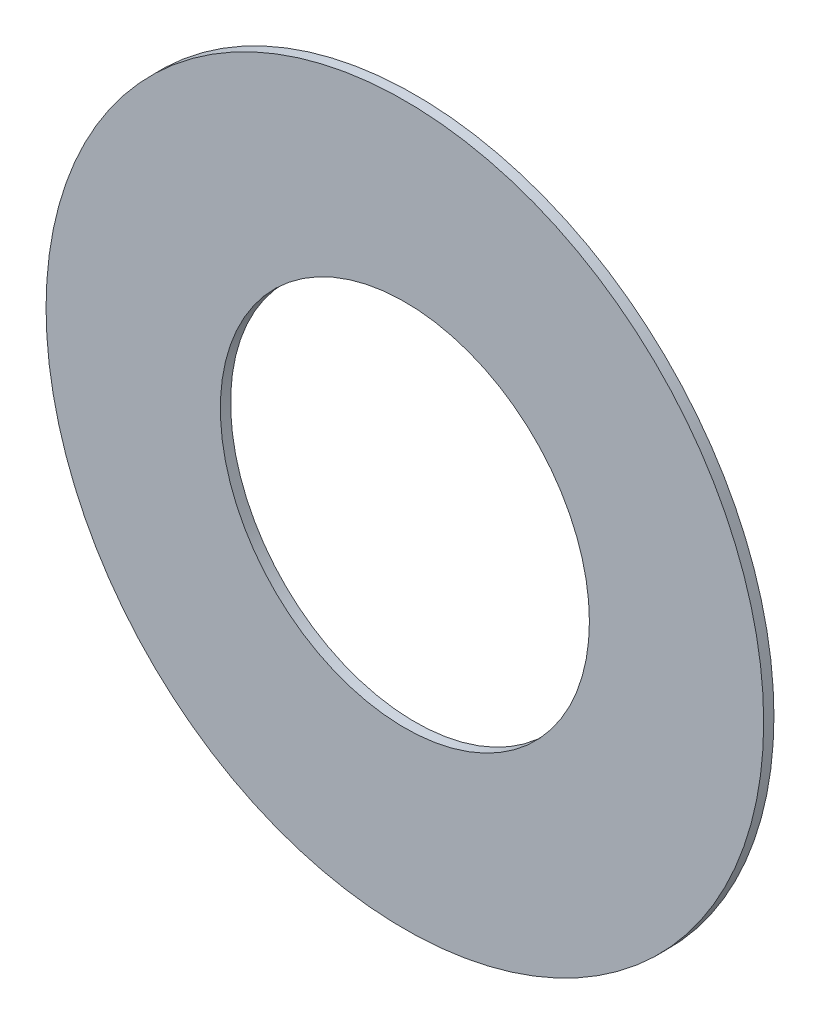
SolidWorks part; units mm, degrees
ref_plane "Front Plane" through (0, 0, 0) normal (0, 0, 1) x (1, 0, 0)
ref_plane "Top Plane" through (0, 0, 0) normal (0, 1, 0) x (1, 0, 0)
ref_plane "Right Plane" through (0, 0, 0) normal (1, 0, 0) x (0, 0, -1)
sketch "Sketch1" plane through (0, 0, 0) normal (0, 0, 1) x (1, 0, 0)
  circle A0 centre (0, 0) radius 36
  circle A1 centre (0, 0) radius 70
  dimension "D1" = 72
  dimension "D2" = 140
extrude "Boss-Extrude1" add sketch "Sketch1" along normal blind 2
sketch "Sketch2" plane through (0, 0, 0) normal (0, 0, 1) x (1, 0, 0)
  line L0 (0, 0) -> (0, 40) construction
  line L1 (-41, 40) -> (3, 40) construction
  line L2 (-41, 40.5) -> (3, 40.5)
  line L3 (-41, 39.5) -> (3, 39.5)
  circle A0 centre (0, 0) radius 40 construction
  arc A1 (-41, 40.5) -> (-41, 39.5) centre (-41, 40) ccw
  arc A2 (3, 39.5) -> (3, 40.5) centre (3, 40) ccw
  point P6 (-19, 40)
  dimension "D1" = 80
  dimension "Slot_Length_2" = 3
  dimension "D3" = 44
  dimension "D4" = 1
extrude "Cut-Extrude1" cut sketch "Sketch2" along normal blind 1
pattern_circular "CirPattern1" count 18 over 360 about axis through (0, 0, 0) along (0, 0, 1) of "Cut-Extrude1"
sketch "Sketch3" plane through (0, 0, 0) normal (0, 0, -1) x (-1, 0, 0)
  line L0 (-3, 40.5) -> (-3, 40.9431) construction
  line L1 (25.0176, 51.1407) -> (-16.3289, 36.0918) construction
